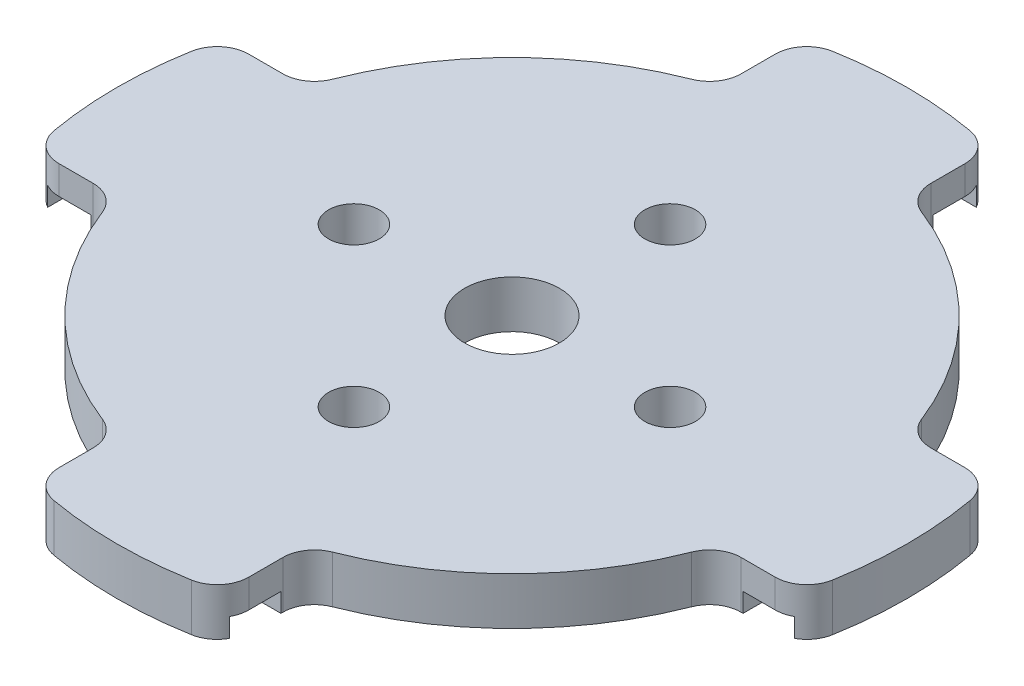
SolidWorks part; units mm, degrees
material "A-Glasfaser"
ref_plane "Ebene vorne" through (0, 0, 0) normal (0, 0, 1) x (1, 0, 0)
ref_plane "Ebene oben" through (0, 0, 0) normal (0, 1, 0) x (1, 0, 0)
ref_plane "Ebene rechts" through (0, 0, 0) normal (1, 0, 0) x (0, 0, -1)
sketch "Skizze1" plane through (0, 0, 0) normal (0, 1, 0) x (1, 0, 0)
  line L0 (-6, 20.4939) -> (-6, 22.6495)
  line L1 (6, 20.4939) -> (6, 22.6495)
  line L3 (0, 25) -> (0, 23.9906) construction
  line L4 (-6, 20.4939) -> (6, 20.4939) construction
  line L5 (20.4939, -6) -> (22.6495, -6)
  line L6 (20.4939, 6) -> (22.6495, 6)
  line L7 (25, 0) -> (0, 0) construction
  line L8 (-6, -20.4939) -> (-6, -22.6495)
  line L9 (6, -20.4939) -> (6, -22.6495)
  line L10 (0, -25) -> (0, 0) construction
  line L11 (-20.4939, 6) -> (-22.6495, 6)
  line L12 (-20.4939, -6) -> (-22.6495, -6)
  line L13 (-25, 0) -> (0, 0) construction
  line L14 (0, 10) -> (-10, 0) construction
  line L15 (-10, 0) -> (0, -10) construction
  line L16 (0, -10) -> (10, 0) construction
  line L17 (10, 0) -> (0, 10) construction
  line L18 (0, 22.3906) -> (0, 0) construction
  circle A0 centre (0, 0) radius 19
  arc A1 (-7.2727, 18.6308) -> (-18.6308, 7.2727) centre (0, 0) ccw
  circle A2 centre (0, 0) radius 1.6
  arc A3 (4.3478, 24.619) -> (-4.3478, 24.619) centre (0, 0) ccw
  arc A4 (-6, 22.6495) -> (-4.3478, 24.619) centre (-4, 22.6495) cw
  arc A5 (-6, 20.4939) -> (-7.2727, 18.6308) centre (-8, 20.4939) cw
  arc A6 (6, 22.6495) -> (4.3478, 24.619) centre (4, 22.6495) ccw
  arc A7 (6, 20.4939) -> (7.2727, 18.6308) centre (8, 20.4939) ccw
  arc A8 (20.4939, -6) -> (18.6308, -7.2727) centre (20.4939, -8) ccw
  arc A9 (22.6495, -6) -> (24.619, -4.3478) centre (22.6495, -4) ccw
  arc A10 (24.619, -4.3478) -> (24.619, 4.3478) centre (0, 0) ccw
  arc A11 (22.6495, 6) -> (24.619, 4.3478) centre (22.6495, 4) cw
  arc A12 (20.4939, 6) -> (18.6308, 7.2727) centre (20.4939, 8) cw
  arc A13 (-6, -20.4939) -> (-7.2727, -18.6308) centre (-8, -20.4939) ccw
  arc A14 (-6, -22.6495) -> (-4.3478, -24.619) centre (-4, -22.6495) ccw
  arc A15 (-4.3478, -24.619) -> (4.3478, -24.619) centre (0, 0) ccw
  arc A16 (6, -22.6495) -> (4.3478, -24.619) centre (4, -22.6495) cw
  arc A17 (6, -20.4939) -> (7.2727, -18.6308) centre (8, -20.4939) cw
  arc A18 (-20.4939, 6) -> (-18.6308, 7.2727) centre (-20.4939, 8) ccw
  arc A19 (-22.6495, 6) -> (-24.619, 4.3478) centre (-22.6495, 4) ccw
  arc A20 (-24.619, 4.3478) -> (-24.619, -4.3478) centre (0, 0) ccw
  arc A21 (-22.6495, -6) -> (-24.619, -4.3478) centre (-22.6495, -4) cw
  arc A22 (-20.4939, -6) -> (-18.6308, -7.2727) centre (-20.4939, -8) cw
  circle A23 centre (0, 10) radius 1.6
  circle A24 centre (10, 0) radius 1.6
  circle A25 centre (-10, 0) radius 1.6
  circle A26 centre (0, -10) radius 1.6
  arc A27 (-18.6308, -7.2727) -> (-7.2727, -18.6308) centre (0, 0) ccw
  arc A28 (18.6308, 7.2727) -> (7.2727, 18.6308) centre (0, 0) ccw
  arc A29 (7.2727, -18.6308) -> (18.6308, -7.2727) centre (0, 0) ccw
  point P20 (0, 20.4939)
  point P68 (-6, 21.5717)
  dimension "D1" = 40
  dimension "D2" = 38
  dimension "D3" = 3.2
  dimension "D4" = 50
  dimension "D5" = 2
  dimension "D6" = 12
  dimension "D8" = 10
  dimension "D7" = 4
extrude "Aufsatz-Linear austragen1" add sketch "Skizze1" along normal blind 3 contours A0 A26 A25 A24 A23 A2 | A17 A29 A8 L5 A9 A10 A11 L6 A12 A28 A7 L1 A6 A3 A4 L0 A5 A1 A18 L11 A19 A20 A21 L12 A22 A27 A13 L8 A14 A15 A16 L9 A0
sketch "Skizze6" plane through (0, 0, 0) normal (0, -1, 0) x (1, 0, 0)
  circle A0 centre (0, 0) radius 3
  dimension "D1" = 6
extrude "Schnitt-Linear austragen2" cut sketch "Skizze6" against normal through all
sketch "Skizze7" plane through (0, 0, 0) normal (0, -1, 0) x (1, 0, 0)
  line L0 (-20.4939, -6) -> (-22.6495, -6) construction
  line L1 (-23.619, 6) -> (-20.619, 6)
  line L2 (-23.619, 6) -> (-23.619, -6)
  line L3 (-23.619, -6) -> (-20.619, -6)
  line L4 (-20.619, 6) -> (-20.619, -6)
  line L5 (-20.4939, 6) -> (-22.6495, 6) construction
  line L6 (6, 23.619) -> (6, 20.619)
  line L7 (6, 23.619) -> (-6, 23.619)
  line L8 (6, 20.619) -> (-6, 20.619)
  line L9 (-6, 23.619) -> (-6, 20.619)
  line L10 (23.619, -6) -> (20.619, -6)
  line L11 (23.619, -6) -> (23.619, 6)
  line L12 (20.619, -6) -> (20.619, 6)
  line L13 (23.619, 6) -> (20.619, 6)
  line L14 (-6, -23.619) -> (-6, -20.619)
  line L15 (-6, -23.619) -> (6, -23.619)
  line L16 (-6, -20.619) -> (6, -20.619)
  line L17 (6, -23.619) -> (6, -20.619)
  point P24 (0, 0)
  dimension "D1" = 1
  dimension "D2" = 3
  dimension "D3" = 0
  dimension "D4" = 0
  dimension "D6" = 0
  dimension "D5" = 4
extrude "Schnitt-Linear austragen3" cut sketch "Skizze7" against normal blind 1.2
